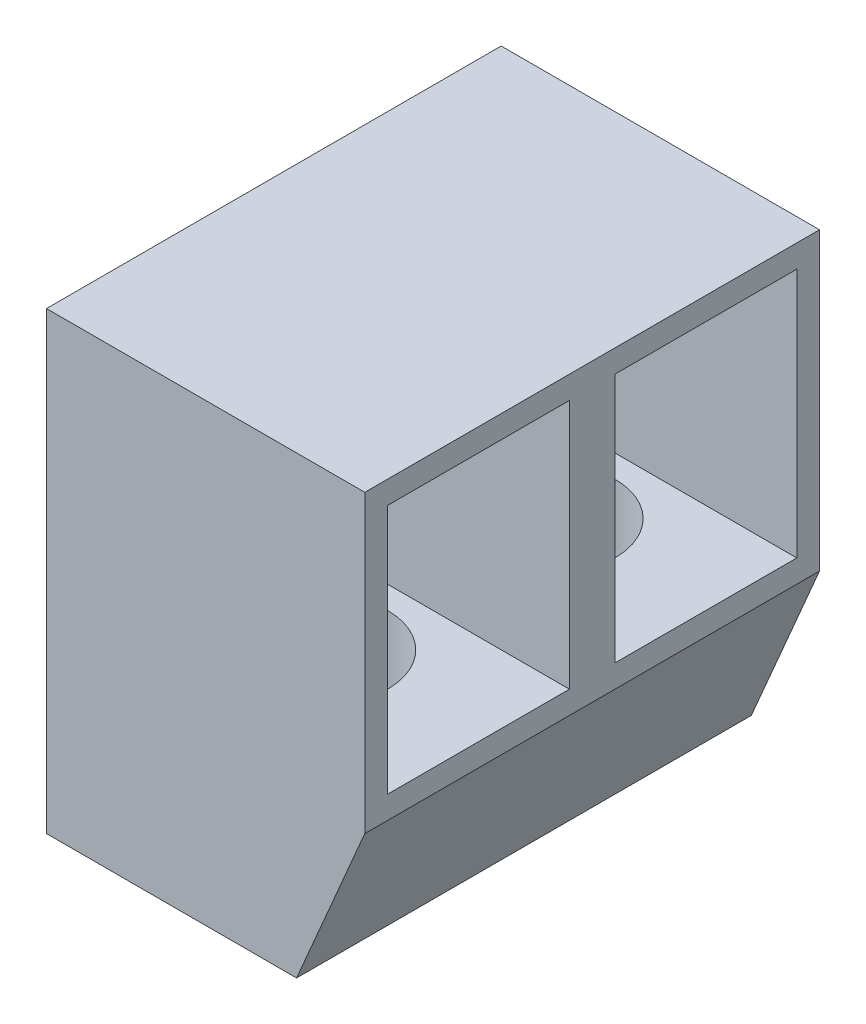
SolidWorks part; units mm, degrees
material "ABS"
ref_plane "Front Plane" through (0, 0, 0) normal (0, 0, 1) x (1, 0, 0)
ref_plane "Top Plane" through (0, 0, 0) normal (0, 1, 0) x (1, 0, 0)
ref_plane "Right Plane" through (0, 0, 0) normal (1, 0, 0) x (0, 0, -1)
sketch "Sketch1" plane through (0, 0, 0) normal (0, 0, 1) x (1, 0, 0)
  line L0 (0, 0) -> (0, 10)
  line L1 (0, 10) -> (7, 10)
  line L2 (7, 10) -> (7, 3.5)
  line L3 (7, 3.5) -> (5.5, 0)
  line L4 (5.5, 0) -> (0, 0)
  dimension "D1" = 10
  dimension "D2" = 7
  dimension "D3" = 5.5
  dimension "D4" = 6.5
extrude "Boss-Extrude1" add sketch "Sketch1" along normal blind 10
sketch "Sketch2" plane through (7, 0, 0) normal (1, 0, 0) x (0, 0, -1)
  line L0 (-10, 3.5) -> (-10, 10) construction
  line L1 (-9.5, 9.5) -> (-5.5, 9.5)
  line L2 (-9.5, 9.5) -> (-9.5, 4)
  line L3 (-9.5, 4) -> (-5.5, 4)
  line L4 (-5.5, 9.5) -> (-5.5, 4)
  line L5 (-4.5, 9.5) -> (-0.5, 9.5)
  line L6 (-4.5, 9.5) -> (-4.5, 4)
  line L7 (-4.5, 4) -> (-0.5, 4)
  line L8 (-0.5, 9.5) -> (-0.5, 4)
  line L9 (0, 3.5) -> (0, 10) construction
  point P8 (-10, 6.75)
  point P11 (-9.5, 6.75)
  dimension "D1" = 5.5
  dimension "D2" = 4
  dimension "D3" = 0.5
  dimension "D4" = 0.5
extrude "Cut-Extrude1" cut sketch "Sketch2" against normal up to next
sketch "Sketch3" plane through (0, 4, 0) normal (0, 1, 0) x (1, 0, 0)
  line L0 (7, 0) -> (0, 0) construction
  line L1 (0, -0.5) -> (0, -4.5) construction
  line L2 (0, -5.5) -> (0, -9.5) construction
  circle A0 centre (3.5, -2.5) radius 1.5
  circle A1 centre (3.5, -7.5) radius 1.5
  point P7 (3.5, 0)
  point P12 (0, -2.5)
  point P16 (0, -7.5)
  dimension "D1" = 3
extrude "Cut-Extrude2" cut sketch "Sketch3" against normal up to next
equation "\"D4@Sketch2\"=\"D3@Sketch2\""
